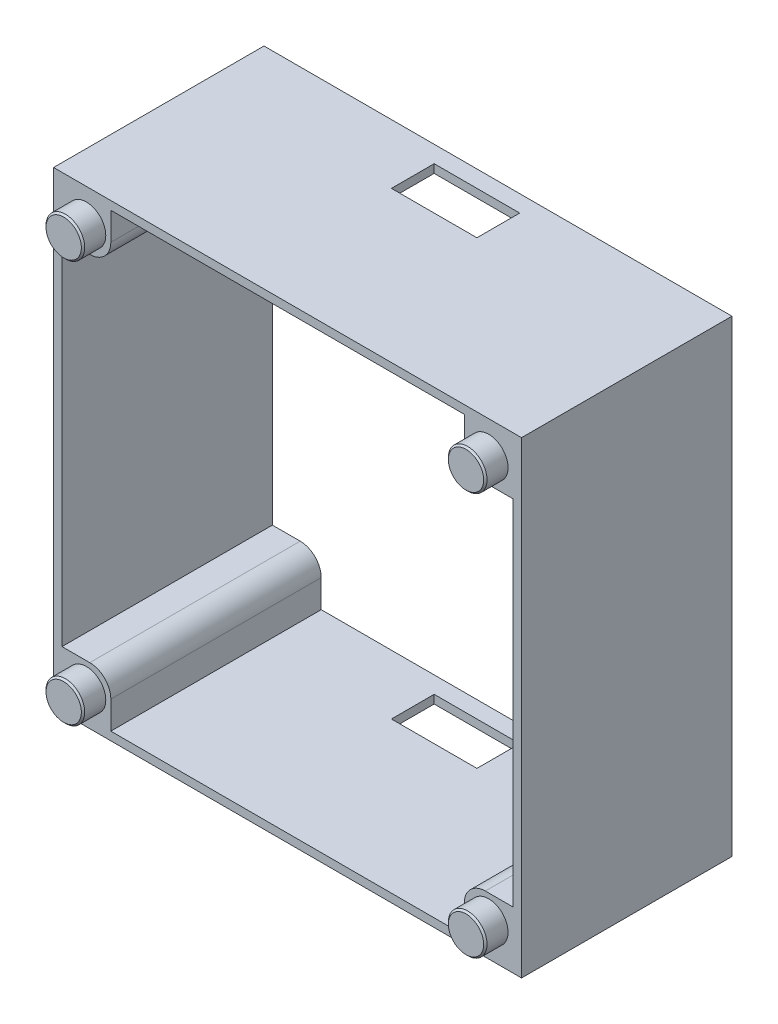
SolidWorks part; units mm, degrees
ref_plane "Přední rovina" through (0, 0, 0) normal (0, 0, 1) x (1, 0, 0)
ref_plane "Horní rovina" through (0, 0, 0) normal (0, 1, 0) x (1, 0, 0)
ref_plane "Pravá rovina" through (0, 0, 0) normal (1, 0, 0) x (0, 0, -1)
sketch "Skica1" plane through (0, 0, 0) normal (0, 0, 1) x (1, 0, 0)
  line L0 (21, -27.8) -> (21, -21)
  line L1 (-27.8, 27.8) -> (27.8, 27.8)
  line L2 (-27.8, 27.8) -> (-27.8, -27.8)
  line L3 (-27.8, -27.8) -> (27.8, -27.8)
  line L4 (27.8, 27.8) -> (27.8, -27.8)
  line L5 (-27.8, 27.8) -> (27.8, -27.8) construction
  line L6 (-27.8, -27.8) -> (27.8, 27.8) construction
  line L7 (-26.8, 26.8) -> (26.8, 26.8)
  line L8 (-26.8, 26.8) -> (-26.8, -26.8)
  line L9 (-26.8, -26.8) -> (26.8, -26.8)
  line L10 (26.8, 26.8) -> (26.8, -26.8)
  line L11 (-26.8, 26.8) -> (26.8, -26.8) construction
  line L12 (-26.8, -26.8) -> (26.8, 26.8) construction
  line L13 (-27.8, 27.8) -> (-21, 27.8)
  line L14 (-27.8, 27.8) -> (-27.8, 21)
  line L15 (-27.8, 21) -> (-21, 21)
  line L16 (-21, 27.8) -> (-21, 21)
  line L17 (27.8, -21) -> (21, -21)
  line L18 (27.8, -27.8) -> (27.8, -21)
  line L19 (27.8, -27.8) -> (21, -27.8)
  line L20 (27.8, 27.8) -> (21, 27.8)
  line L21 (27.8, 27.8) -> (27.8, 21)
  line L22 (27.8, 21) -> (21, 21)
  line L23 (21, 27.8) -> (21, 21)
  line L24 (27.8, -27.8) -> (27.8, -21)
  line L25 (27.8, -27.8) -> (21, -27.8)
  line L26 (21, -27.8) -> (21, -21)
  line L27 (27.8, -21) -> (21, -21)
  line L28 (-27.8, -27.8) -> (-21, -27.8)
  line L29 (-27.8, -27.8) -> (-27.8, -21)
  line L30 (-27.8, -21) -> (-21, -21)
  line L31 (-21, -27.8) -> (-21, -21)
  point P0 (0, 0)
  point P5 (0, 0)
  point P32 (0, 0)
  dimension "D1" = 55.6
  dimension "D2" = 53.6
  dimension "D3" = 6.8
  dimension "D4" = 4
extrude "Přidat vysunutím2" add sketch "Skica1" along normal blind 25 contours L16 L1 L2 L15 L8 L7 | L16 L7 L8 L15 | L1 L23 L7 L10 L22 L4 | L7 L23 L22 L10 | L4 L17 L10 L9 L0 L3 | L10 L17 L0 L9 | L9 L31 L30 L8 | L3 L31 L9 L8 L30 L2 | L2 L30 L8 L15 | L31 L3 L0 L9 | L4 L22 L10 L17 | L23 L1 L16 L7
fillet "Zaoblit1" radius 2.5 4 edges at (-21, -21, 12.5) (21, -21, 12.5) (21, 21, 12.5) (-21, 21, 12.5)
sketch "Skica2" plane through (0, 0, 0) normal (0, 0, -1) x (-1, 0, 0)
  line L0 (-27.8, 27.8) -> (-27.8, -27.8) construction
  line L1 (27.8, 27.8) -> (-27.8, 27.8) construction
  circle A0 centre (-23.9, 23.9) radius 2.4
  circle A4 centre (23.9, 23.9) radius 2.4
  circle A5 centre (23.9, -23.9) radius 2.4
  circle A6 centre (-23.9, -23.9) radius 2.4
  point P15 (-0.2487, -0.2461)
  point P16 (0, 0)
  dimension "D1" = 4.8
  dimension "D2" = 3.9
  dimension "D3" = 3.9
  dimension "D4" = 4
extrude "Odebrat vysunutím1" cut sketch "Skica2" against normal blind 1.9
sketch "Skica3" plane through (0, 0, 25) normal (0, 0, 1) x (1, 0, 0)
  line L0 (-27.8, 27.8) -> (-27.8, -27.8) construction
  line L1 (-27.8, 27.8) -> (27.8, 27.8) construction
  circle A0 centre (-23.9, 23.9) radius 2.3
  circle A4 centre (23.9, 23.9) radius 2.3
  circle A5 centre (23.9, -23.9) radius 2.3
  circle A6 centre (-23.9, -23.9) radius 2.3
  point P15 (-0.5, 0)
  point P16 (0, 0)
  dimension "D1" = 4.6
  dimension "D2" = 3.9
  dimension "D3" = 3.9
  dimension "D4" = 4
extrude "Přidat vysunutím3" add sketch "Skica3" along normal blind 2.7
chamfer "Zkosení1" distance 0.2 angle 45 4 edges at (-21.6, 23.9, 27.7) (-21.6, -23.9, 27.7) (26.2, -23.9, 27.7) (26.2, 23.9, 27.7)
sketch "Skica4" plane through (0, -27.8, 0) normal (0, -1, 0) x (-1, 0, 0)
  line L0 (27.8, -25) -> (27.8, 0) construction
  line L1 (5.58, -7.08) -> (-4.58, -7.08)
  line L2 (5.58, -7.08) -> (5.58, -2)
  line L3 (5.58, -2) -> (-4.58, -2)
  line L4 (-4.58, -7.08) -> (-4.58, -2)
  line L5 (-27.8, -25) -> (-27.8, 0) construction
  line L6 (27.8, 0) -> (-27.8, 0) construction
  dimension "D1" = 5.08
  dimension "D2" = 10.16
  dimension "D3" = 22.22
  dimension "D4" = 23.22
  dimension "D5" = 2
extrude "Odebrat vysunutím2" cut sketch "Skica4" against normal blind 68.7
